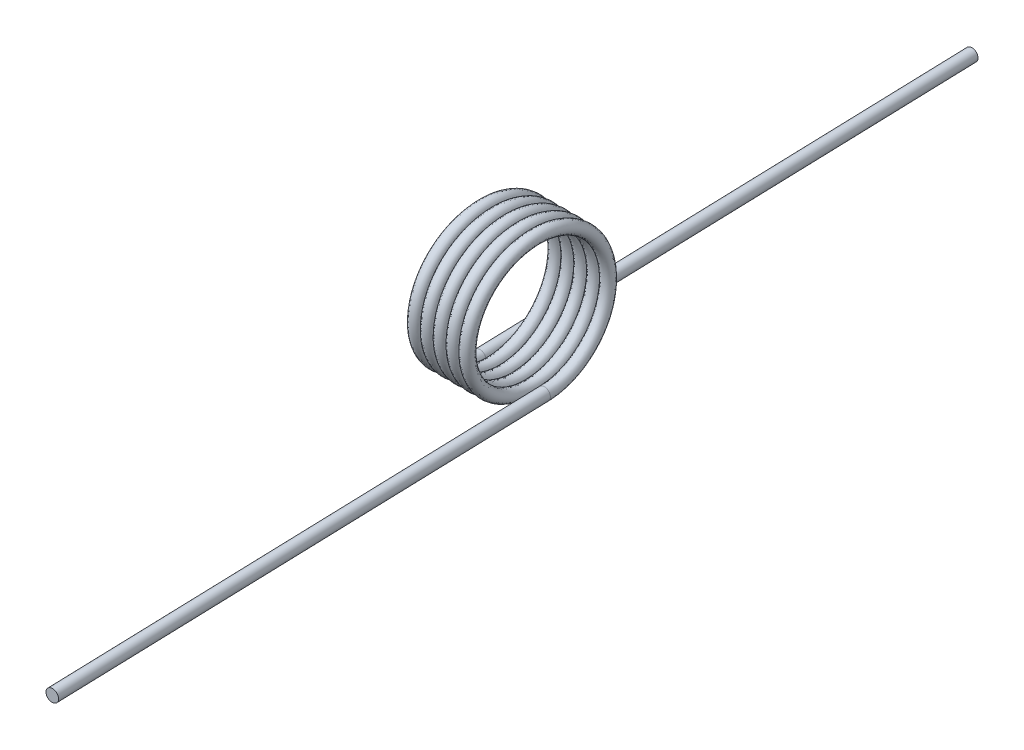
SolidWorks part; units mm, degrees
ref_plane "Front" through (0, 0, 0) normal (0, 0, 1) x (1, 0, 0)
ref_plane "Top" through (0, 0, 0) normal (0, 1, 0) x (1, 0, 0)
ref_plane "Right" through (0, 0, 0) normal (1, 0, 0) x (0, 0, -1)
sketch "Sketch1" plane through (0, 0, 0) normal (1, 0, 0) x (0, 0, -1)
  line L0 (0, -2.286) -> (0, -2.7432) construction
  line L1 (0, -2.7432) -> (19.05, -2.7432) construction
  line L2 (0, -2.7432) -> (-19.05, -2.7432) construction
  line L3 (0, 0) -> (2.7432, 0) construction
  line L4 (0, 0) -> (0, -2.7432) construction
  line L5 (-19.05, -2.7432) -> (-19.05, -2.286) construction
  line L6 (-19.05, -2.286) -> (0, -2.286) construction
  line L7 (19.05, -2.7432) -> (19.05, -2.286) construction
  line L8 (19.05, -2.286) -> (0, -2.286) construction
  circle A0 centre (0, 0) radius 2.7432 construction
  circle A1 centre (0, 0) radius 1.778 construction
  circle A2 centre (0, 0) radius 2.5146 construction
  point P7 (0, -2.5146)
  point P10 (0, 2.7432)
  dimension "OD" = 5.4864
  dimension "For Shaft Diameter" = 3.556
  dimension "Wire Diameter" = 0.4572
  dimension "Leg Length" = 19.05
  dimension "Deflection Angle" = 180
sketch "Sketch2" plane through (0, 0, 0) normal (1, 0, 0) x (0, 0, -1)
  circle A0 centre (0, 0) radius 2.5146 construction
  circle A2 centre (0, 0) radius 2.5146
curve "Helix/Spiral1" pitch 0.4826 height 2.413 turns 5
ref_plane "Plane1" through (0, -2.5146, 0) normal (-0.0305, 0, -0.9995) x (0.9993, -0.0232, -0.0305)
sketch "Sketch3" plane through (0, -2.5146, 0) normal (-0.0305, 0, -0.9995) x (0.9993, -0.0232, -0.0305)
  circle A0 centre (0, 0) radius 0.2286
  dimension "D1" = 0.4572
sweep "Sweep1" add profiles "Sketch3" path "Helix/Spiral1"
sketch "Sketch4" plane through (0, 0, 0) normal (0.0305, 0, 0.9995) x (-0.9993, 0.0232, 0.0305)
  circle A1 centre (-0.0584, 2.5139) radius 0.2286
  circle A2 centre (-0.0584, 2.5139) radius 0.2286
  dimension "D1" = 0
extrude "Extrude1" add sketch "Sketch4" along normal blind 19.05
sketch "Sketch5" plane through (-0.0022, 0, -0.0736) normal (-0.0305, 0, -0.9995) x (0.9986, 0.0436, -0.0305)
  circle A1 centre (-2.5192, 2.4071) radius 0.2286
  circle A2 centre (-2.5192, 2.4071) radius 0.2286
  dimension "D1" = 0
extrude "Extrude2" add sketch "Sketch5" along normal blind 19.05
sketch "Sketch6" plane through (0, 0, 0) normal (1, 0, 0) x (0, 0, -1)
  circle A2 centre (0, 0) radius 2.286 construction
equation "\"D4@Helix/Spiral1\" = \"Wire Diameter@Sketch1\" + .001"
equation "\"D1@Sketch3\"=\"Wire Diameter@Sketch1\""
equation "\"D1@Extrude2\"=\"Leg Length@Sketch1\""
equation "\"Leg Length@Extrude1\"=\"Leg Length@Sketch1\""
